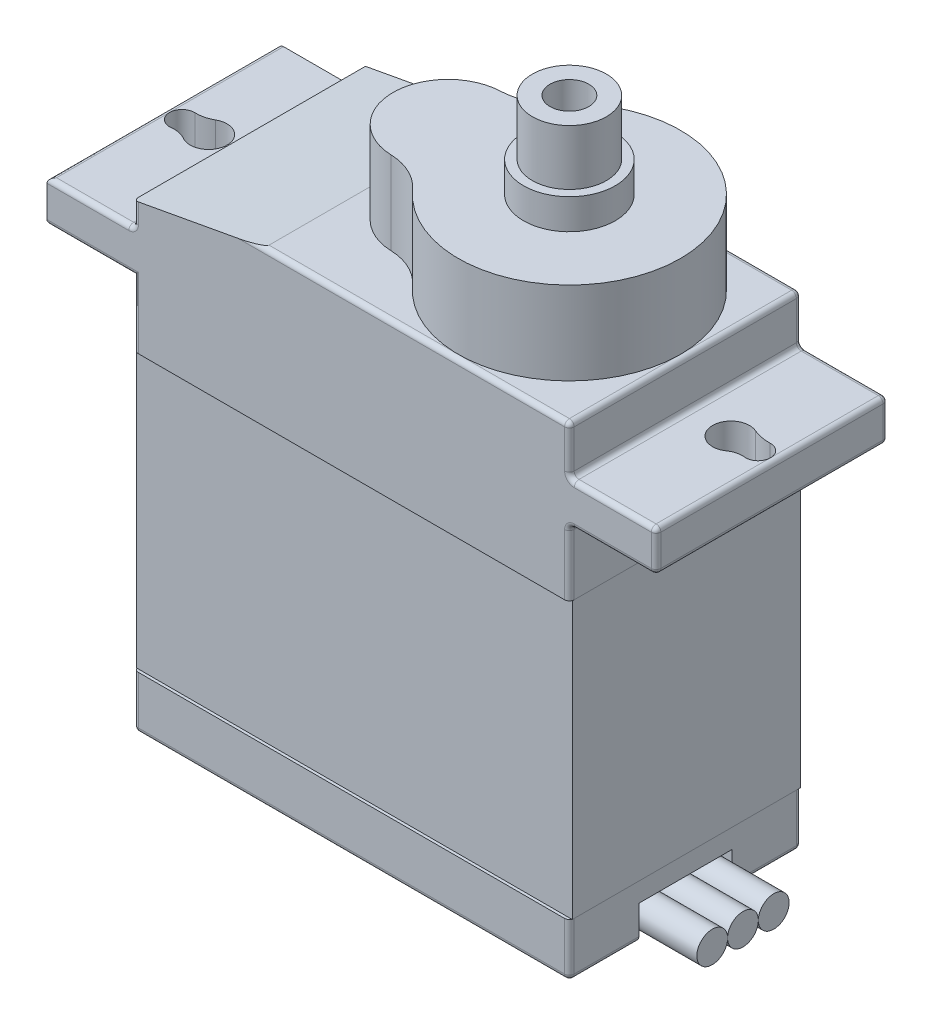
SolidWorks part; units mm, degrees
ref_plane "Alzado" through (0, 0, 0) normal (0, 0, 1) x (1, 0, 0)
ref_plane "Planta" through (0, 0, 0) normal (0, 1, 0) x (1, 0, 0)
ref_plane "Vista lateral" through (0, 0, 0) normal (1, 0, 0) x (0, 0, -1)
sketch "Croquis1" plane through (0, 0, 0) normal (0, 1, 0) x (1, 0, 0)
  line L1 (-11.335, 6.03) -> (11.335, 6.03)
  line L2 (-11.335, 6.03) -> (-11.335, -6.03)
  line L3 (-11.335, -6.03) -> (11.335, -6.03)
  line L4 (11.335, 6.03) -> (11.335, -6.03)
  line L5 (-11.335, 6.03) -> (11.335, -6.03) construction
  line L6 (-11.335, -6.03) -> (11.335, 6.03) construction
  point P0 (0, 0)
  dimension "D1" = 22.67
  dimension "D2" = 12.06
extrude "Saliente-Extruir1" add sketch "Croquis1" along normal blind 25.15
sketch "Croquis2" plane through (11.335, 0, 0) normal (1, 0, 0) x (0, 0, -1)
  line L0 (-6.03, 0) -> (-6.03, 20.53) construction
  line L1 (-6.03, 25.15) -> (-6.03, 0) construction
  line L2 (-6.03, 20.53) -> (6.03, 20.53)
  line L3 (6.03, 25.15) -> (6.03, 0) construction
  line L4 (-6.03, 22.66) -> (6.03, 22.66)
  line L5 (-6.03, 22.66) -> (-6.03, 20.53)
  line L6 (6.03, 22.66) -> (6.03, 20.53)
  dimension "D1" = 20.53
  dimension "D2" = 2.13
extrude "Saliente-Extruir2" add sketch "Croquis2" along normal blind 4.51
sketch "Croquis5" plane through (-11.335, 0, 0) normal (-1, 0, 0) x (0, 0, 1)
  line L1 (6.03, 25.15) -> (6.03, 0) construction
  line L2 (-6.03, 22.66) -> (6.03, 22.66)
  line L3 (-6.03, 22.66) -> (-6.03, 20.53)
  line L4 (-6.03, 20.53) -> (6.03, 20.53)
  line L5 (6.03, 22.66) -> (6.03, 20.53)
  line L8 (-6.03, 0) -> (6.03, 0) construction
  dimension "D1" = 20.53
extrude "Saliente-Extruir3" add sketch "Croquis5" along normal blind 4.51
fillet "Redondeo1" radius 0.25 30 edges at (11.335, 0, 0) (0, 0, -6.03) (0, 0, 6.03) (-11.335, 0, 0) (0, 25.15, -6.03) (0, 25.15, 6.03) (-11.335, 25.15, 0) (11.335, 25.15, 0) (15.845, 21.595, -6.03) (15.845, 21.595, 6.03) (15.845, 20.53, 0) (15.845, 22.66, 0) (-15.845, 20.53, 0) (-15.845, 22.66, 0)
sketch "Croquis6" plane through (0, 22.66, 0) normal (0, 1, 0) x (1, 0, 0)
  line L0 (-15.595, 6.03) -> (-11.585, -5.78) construction
  line L1 (-11.585, -5.78) -> (-11.585, 6.03) construction
  line L2 (-11.585, 6.03) -> (-15.595, -5.78) construction
  line L3 (0, 0) -> (0, 5.78) construction
  line L4 (11.085, 5.78) -> (-11.085, 5.78) construction
  line L5 (0, 5.78) -> (0, -5.78) construction
  line L6 (-11.085, -5.78) -> (11.085, -5.78) construction
  line L9 (-15.595, 6.03) -> (-15.595, -5.78) construction
  arc A0 (-14.0754, -0.7033) -> (-14.0683, 0.9574) centre (-13.59, 0.125) ccw
  arc A1 (14.1493, -0.6553) -> (13.9681, 1.0074) centre (13.59, 0.125) cw
  arc A2 (-14.9216, 0.7478) -> (-14.8659, -0.5415) centre (-14.9475, 0.1009) ccw
  arc A3 (14.8717, -0.4691) -> (14.9323, 0.8213) centre (14.9475, 0.1739) ccw
  arc A4 (-14.9216, 0.7478) -> (-14.0683, 0.9574) centre (-14.8582, 2.332) ccw
  arc A5 (-14.8659, -0.5415) -> (-14.0754, -0.7033) centre (-14.7082, -1.7831) cw
  arc A6 (13.9681, 1.0074) -> (14.9323, 0.8213) centre (14.8781, 3.1309) ccw
  arc A7 (14.1493, -0.6553) -> (14.8717, -0.4691) centre (14.7507, -1.4944) cw
  dimension "D1" = 1.92
extrude "Cortar-Extruir12" cut sketch "Croquis6" against normal blind 4.51
sketch "Croquis8" plane through (0, 25.15, 0) normal (0, 1, 0) x (1, 0, 0)
  line L0 (11.085, 0) -> (-11.085, 0) construction
  line L3 (11.085, -5.78) -> (11.085, 5.78) construction
  line L4 (-11.085, 5.78) -> (-11.085, -5.78) construction
  line L5 (11.085, 5.78) -> (-11.085, 5.78) construction
  line L6 (11.085, 0) -> (-1.015, 0) construction
  arc A0 (0.9947, -3.8509) -> (0.9947, 3.8509) centre (5.305, 0) ccw
  arc A1 (-1.1194, 2.8581) -> (-1.1194, -2.8581) centre (-1.015, 0) ccw
  arc A2 (-1.1194, -2.8581) -> (0.9947, -3.8509) centre (-1.2281, -5.8368) cw
  arc A3 (-1.1194, 2.8581) -> (0.9947, 3.8509) centre (-1.2281, 5.8368) ccw
  dimension "D1" = 5.72
  dimension "D2" = 6.32
extrude "Saliente-Extruir4" add sketch "Croquis8" along normal blind 4.32 separate body
sketch "Croquis9" plane through (0, 29.47, 0) normal (0, 1, 0) x (1, 0, 0)
  line L0 (5.305, 5.78) -> (5.305, 0) construction
  line L1 (11.085, 5.78) -> (-11.085, 5.78) construction
  arc A0 (0.9947, -3.8509) -> (0.9947, 3.8509) centre (5.305, 0) ccw construction
  circle A1 centre (5.305, 0) radius 2.385
  dimension "D1" = 4.77
extrude "Saliente-Extruir5" add sketch "Croquis9" along normal blind 1.58 separate body
sketch "Croquis10" plane through (0, 31.05, 0) normal (0, 1, 0) x (1, 0, 0)
  circle A0 centre (5.305, 0) radius 2.385
extrude "Saliente-Extruir6" add sketch "Croquis10" along normal blind 2.88 separate body
sketch "Croquis11" plane through (0, 33.93, 0) normal (0, 1, 0) x (1, 0, 0)
  circle A0 centre (5.305, 0) radius 1.01
  dimension "D1" = 2.02
extrude "Cortar-Extruir13" cut sketch "Croquis11" against normal blind 3.88
sketch "Croquis12" plane through (0, 33.93, 0) normal (0, 1, 0) x (1, 0, 0)
  circle A2 centre (5.305, 0) radius 1.925
  circle A3 centre (5.305, 0) radius 2.385
  dimension "D4" = 3.85
extrude "Cortar-Extruir14" cut sketch "Croquis12" along a picked direction on the side against the normal blind 2.88
sketch "Croquis13" plane through (0, 0, 6.03) normal (0, 0, 1) x (1, 0, 0)
  line L0 (-4.5405, 25.15) -> (-11.335, 23.905) construction
  line L1 (-11.085, 25.15) -> (11.085, 25.15) construction
  line L2 (-11.335, 22.91) -> (-11.335, 24.9) construction
  line L3 (-4.5405, 25.15) -> (-11.335, 23.905)
  line L4 (-11.335, 23.905) -> (-11.335, 25.15)
  line L5 (-11.335, 25.15) -> (-4.5405, 25.15)
extrude "Cortar-Extruir15" cut sketch "Croquis13" against normal blind 16.88
sketch "Croquis14" plane through (0, 0, 6.03) normal (0, 0, 1) x (1, 0, 0)
  line L0 (-11.085, 17.1) -> (11.085, 17.1)
  line L1 (-11.085, 20.78) -> (-11.085, 0.25) construction
  line L2 (11.085, 0.25) -> (11.085, 20.28) construction
  line L3 (11.085, 24.9) -> (-5.9049, 24.9) construction
  line L4 (-11.085, 2.77) -> (11.085, 2.77)
  line L5 (-11.085, 0.25) -> (11.085, 0.25) construction
  line L6 (11.085, 17.1) -> (11.085, 2.77)
  line L7 (-11.085, 17.1) -> (-11.085, 2.77)
  dimension "D1" = 7.8
  dimension "D2" = 2.52
extrude "Cortar-Extruir16" cut sketch "Croquis14" against normal blind 16.88
sketch "Croquis16" plane through (-11.335, 0, 0) normal (-1, 0, 0) x (0, 0, 1)
  line L0 (5.78, 17.1096) -> (-5.78, 17.1096)
  line L3 (5.78, 0.25) -> (5.78, 20.53) construction
  line L4 (-5.78, 20.53) -> (-5.78, 0.25) construction
  line L5 (-5.78, 2.7548) -> (5.78, 2.7548)
  line L6 (5.78, 17.1096) -> (5.78, 2.7548)
  line L7 (-5.78, 2.7548) -> (-5.78, 17.1096)
extrude "Cortar-Extruir17" cut sketch "Croquis16" against normal blind 27.88
sketch "Croquis17" plane through (0, 0, 0) normal (0, 0, 1) x (1, 0, 0)
  line L0 (-11.335, 17.1096) -> (11.335, 17.1096)
  line L1 (11.335, 17.1096) -> (11.335, 2.7548)
  line L2 (11.335, 2.7548) -> (-11.335, 2.7548)
  line L3 (-11.335, 2.7548) -> (-11.335, 17.1096)
extrude "Cortar-Extruir18" cut sketch "Croquis17" against normal blind 27.88 and the other way blind 27.88
sketch "Croquis18" plane through (0, 0, 0) normal (0, 0, 1) x (1, 0, 0)
  line L0 (-11.335, 17.1096) -> (-11.335, 2.7548)
  line L1 (-11.335, 2.7548) -> (11.335, 2.7548)
  line L2 (11.335, 2.7548) -> (11.335, 17.1096)
  line L3 (11.335, 17.1096) -> (-11.335, 17.1096)
extrude "Saliente-Extruir7" add sketch "Croquis18" along normal blind 5.88 and the other way blind 6 separate body
sketch "Croquis19" plane through (11.335, 0, 0) normal (1, 0, 0) x (0, 0, -1)
  line L0 (5.78, 1.5024) -> (2.42, 1.5024) construction
  line L1 (5.78, 0.25) -> (5.78, 2.7548) construction
  line L2 (0, 2.7548) -> (0, 1.7548) construction
  line L4 (-5.78, 1.5024) -> (-2.42, 1.5024) construction
  line L5 (6, 2.7548) -> (-5.88, 2.7548) construction
  line L6 (-2.42, 1.7548) -> (2.42, 1.7548)
  line L7 (2.42, 1.7548) -> (2.42, 0)
  line L8 (5.78, 0) -> (-5.78, 0) construction
  line L9 (2.42, 0) -> (-2.42, 0)
  line L10 (-2.42, 0) -> (-2.42, 1.7548)
  dimension "D1" = 3.36
  dimension "D2" = 1
extrude "Cortar-Extruir19" cut sketch "Croquis19" against normal blind 1.6
sketch "Croquis20" plane through (9.735, 0, 0) normal (1, 0, 0) x (0, 0, -1)
  line L0 (0, 1.7548) -> (0, 0) construction
  line L1 (2.42, 1.7548) -> (-2.42, 1.7548) construction
  line L2 (0, 0.8774) -> (2.42, 0.8774) construction
  line L3 (2.42, 0) -> (2.42, 1.7548) construction
  line L4 (0, 0.8774) -> (-2.42, 0.8774) construction
  line L5 (-2.42, 1.7548) -> (-2.42, 0) construction
  circle A0 centre (0, 0.8774) radius 0.8
  circle A1 centre (-1.6, 0.8774) radius 0.8
  circle A2 centre (1.6, 0.8774) radius 0.8
  dimension "D1" = 1.6
  dimension "D2" = 1.6
  dimension "D3" = 1.6
extrude "Saliente-Extruir8" add sketch "Croquis20" along normal blind 4.6 separate body contours A1 | A0 | A2
